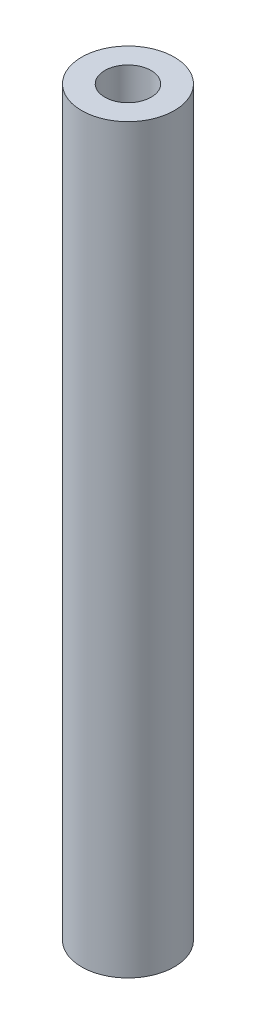
SolidWorks part; units mm, degrees
ref_plane "Front Plane" through (0, 0, 0) normal (0, 0, 1) x (1, 0, 0)
ref_plane "Top Plane" through (0, 0, 0) normal (0, 1, 0) x (1, 0, 0)
ref_plane "Right Plane" through (0, 0, 0) normal (1, 0, 0) x (0, 0, -1)
sketch "Sketch1" plane through (0, 0, 0) normal (0, 1, 0) x (1, 0, 0)
  circle A0 centre (0, 0) radius 2.5
  circle A1 centre (0, 0) radius 5
  dimension "D1" = 5
  dimension "D2" = 10
extrude "Boss-Extrude1" add sketch "Sketch1" along normal blind 80
